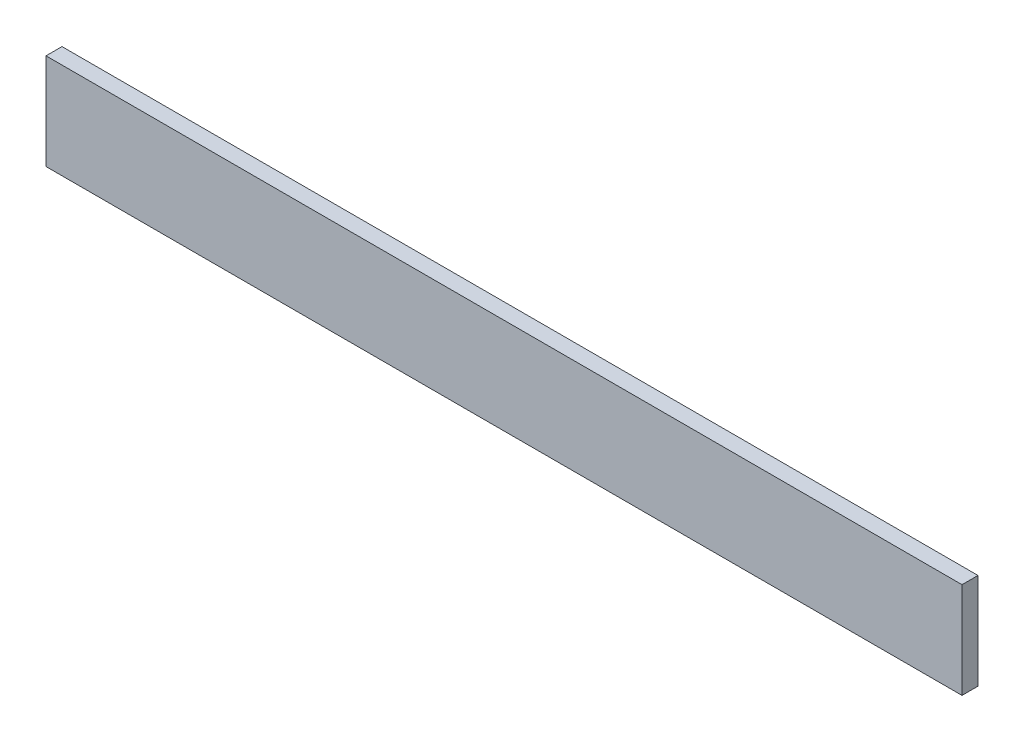
SolidWorks part; units mm, degrees
material "Acrylic (Medium-high impact)"
ref_plane "Front Plane" through (0, 0, 0) normal (0, 0, 1) x (1, 0, 0)
ref_plane "Top Plane" through (0, 0, 0) normal (0, 1, 0) x (1, 0, 0)
ref_plane "Right Plane" through (0, 0, 0) normal (1, 0, 0) x (0, 0, -1)
sketch "Sketch1" plane through (0, 0, 0) normal (0, 0, 1) x (1, 0, 0)
  line L1 (-143.25, 15) -> (143.25, 15)
  line L2 (-143.25, 15) -> (-143.25, -15)
  line L3 (-143.25, -15) -> (143.25, -15)
  line L4 (143.25, 15) -> (143.25, -15)
  line L5 (-143.25, 15) -> (143.25, -15) construction
  line L6 (-143.25, -15) -> (143.25, 15) construction
  circle A0 centre (0, -40) radius 8.5
  point P0 (0, 0)
  dimension "D3" = 17
  dimension "D5" = 143.25
  dimension "D1" = 286.5
  dimension "D2" = 30
  dimension "D4" = 40
extrude "Boss-Extrude1" add sketch "Sketch1" along normal blind 5 contours L4 L1 L2 L3
